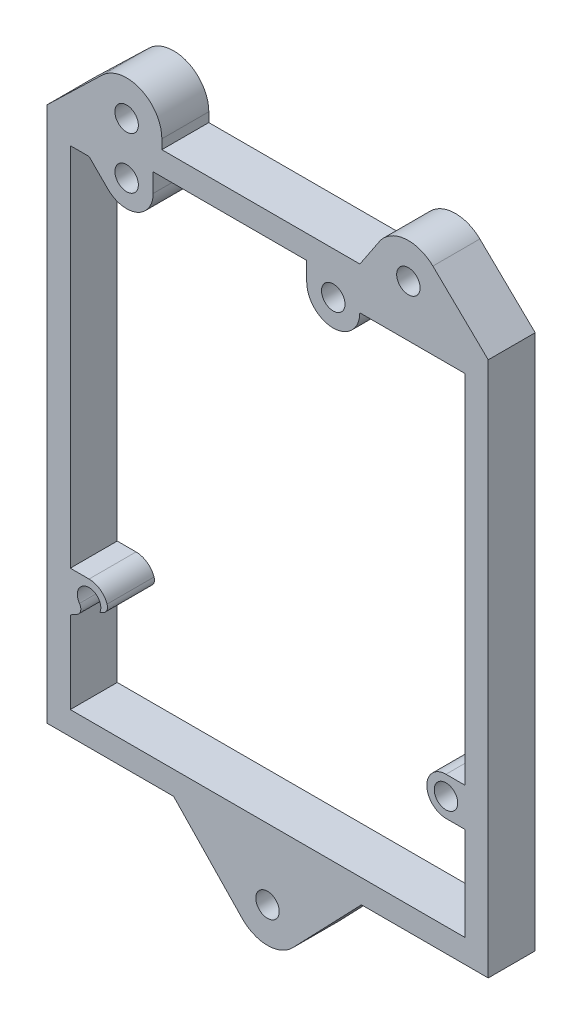
SolidWorks part; units mm, degrees
ref_plane "Front Plane" through (0, 0, 0) normal (0, 0, 1) x (1, 0, 0)
ref_plane "Top Plane" through (0, 0, 0) normal (0, 1, 0) x (1, 0, 0)
ref_plane "Right Plane" through (0, 0, 0) normal (1, 0, 0) x (0, 0, -1)
sketch "Sketch1" plane through (0, 0, 0) normal (0, 0, 1) x (1, 0, 0)
  line L0 (13.97, -3.175) -> (23.2348, -12.8236)
  line L1 (39.37, -3.175) -> (30.1052, -12.8236)
  line L2 (39.37, -3.175) -> (56.515, -3.175)
  line L3 (12.3825, 73.025) -> (12.3825, 71.755)
  line L4 (56.515, 69.215) -> (49.0297, 76.4495)
  line L5 (39.1611, 71.755) -> (41.5921, 75.4003)
  line L6 (-3.175, 69.215) -> (4.3103, 76.4495)
  line L36 (53.34, 66.04) -> (53.34, 0) construction
  line L37 (53.34, 0) -> (0, 0) construction
  line L38 (0, 0) -> (0, 66.04) construction
  line L39 (0, 66.04) -> (2.54, 66.04) construction
  line L43 (40.386, 66.04) -> (53.34, 66.04) construction
  line L44 (-3.175, -3.175) -> (56.515, -3.175)
  line L45 (56.515, -3.175) -> (56.515, 69.215)
  line L46 (-3.175, 69.215) -> (-3.175, -3.175)
  line L47 (1.2249, 69.215) -> (-3.175, 69.215)
  line L48 (3.7649, 71.755) -> (1.2249, 69.215)
  line L49 (39.1611, 71.755) -> (3.7649, 71.755)
  line L50 (41.7011, 69.215) -> (39.1611, 71.755)
  line L51 (56.515, 69.215) -> (41.7011, 69.215)
  line L52 (-3.175, -3.175) -> (13.97, -3.175)
  line L53 (56.515, -3.175) -> (56.515, 69.215)
  line L54 (-3.175, 69.215) -> (-3.175, -3.175)
  line L57 (39.1611, 71.755) -> (12.3825, 71.755)
  line L60 (53.34, 66.04) -> (53.34, 17.8275)
  line L61 (53.34, 0) -> (0, 0)
  line L62 (0, 0) -> (0, 11.0938)
  line L63 (0, 66.04) -> (2.54, 66.04)
  line L64 (26.67, -3.175) -> (26.67, 77.2177) construction
  line L66 (11.2075, 68.58) -> (31.9725, 68.58)
  line L67 (40.386, 66.04) -> (53.34, 66.04)
  line L68 (50.8, 17.8275) -> (53.34, 17.8275)
  line L69 (50.8, 12.6525) -> (53.34, 12.6525)
  line L70 (53.34, 12.6525) -> (53.34, 0)
  line L71 (2.54, 16.5575) -> (0, 16.5575)
  line L72 (5.1275, 13.97) -> (3.9948, 13.3346)
  line L73 (2.3238, 12.3973) -> (0, 11.0938)
  line L74 (0, 16.5575) -> (0, 66.04)
  line L75 (5.08, 63.5065) -> (2.54, 66.04)
  line L76 (11.2075, 66.04) -> (11.2075, 68.58)
  line L77 (39.1475, 66.04) -> (40.386, 66.04)
  line L78 (31.9725, 66.04) -> (31.9725, 68.58)
  circle A0 centre (35.56, 66.04) radius 1.5875 construction
  circle A1 centre (7.62, 66.04) radius 1.5875 construction
  circle A2 centre (2.54, 13.97) radius 1.5875 construction
  circle A3 centre (50.8, 15.24) radius 1.5875 construction
  circle A4 centre (35.56, 66.04) radius 1.5875
  circle A5 centre (7.62, 66.04) radius 1.5875
  arc A6 (3.9948, 13.3346) -> (2.3238, 12.3973) centre (2.54, 13.97) ccw
  circle A7 centre (50.8, 15.24) radius 1.5875
  arc A8 (5.1275, 13.97) -> (2.54, 16.5575) centre (2.54, 13.97) ccw
  arc A9 (50.8, 17.8275) -> (50.8, 12.6525) centre (50.8, 15.24) ccw
  arc A10 (5.08, 63.5065) -> (11.2075, 66.04) centre (7.62, 66.04) ccw
  circle A11 centre (2.54, 13.97) radius 2.5875 construction
  circle A12 centre (2.54, 13.97) radius 1.5875 construction
  arc A13 (31.9725, 66.04) -> (39.1475, 66.04) centre (35.56, 66.04) ccw
  circle A14 centre (26.67, -9.525) radius 1.5875
  circle A15 centre (35.56, 66.04) radius 3.5875 construction
  circle A16 centre (7.62, 66.04) radius 3.5875 construction
  arc A17 (23.2348, -12.8236) -> (30.1052, -12.8236) centre (26.67, -9.525) ccw
  circle A18 centre (45.72, 73.025) radius 1.5875
  circle A19 centre (26.67, -9.525) radius 4.7625 construction
  circle A20 centre (7.62, 73.025) radius 1.5875
  arc A21 (49.0297, 76.4495) -> (41.5921, 75.4003) centre (45.72, 73.025) ccw
  arc A22 (4.3103, 76.4495) -> (12.3825, 73.025) centre (7.62, 73.025) cw
  circle A24 centre (7.62, 73.025) radius 4.7625 construction
  circle A25 centre (45.72, 73.025) radius 4.7625 construction
  point P34 (53.3875, 15.24)
  point P37 (6.1275, 13.97)
  point P41 (4.0581, 14.4341)
  point P47 (11.2075, 66.04)
  point P54 (39.1475, 66.04)
  point P64 (31.4325, -9.525)
  point P74 (50.4825, 73.025)
  point P75 (12.3825, 73.025)
  dimension "D4" = 3.175
  dimension "D8" = 3.175
  dimension "D5" = 6.35
  dimension "D6" = 3.175
  dimension "D7" = 12.7
  dimension "D9" = 19.05
  dimension "D10" = 82.55
  dimension "D1" = 3.175
  dimension "D2" = 1
  dimension "D3" = 2
  dimension "D11" = 3.175
  dimension "D12" = 3.175
extrude "Boss-Extrude1" add sketch "Sketch1" along normal blind 6.35
fillet "Fillet1" radius 1 2 edges at (2.3238, 12.3973, 3.175) (5.1275, 13.97, 3.175)
